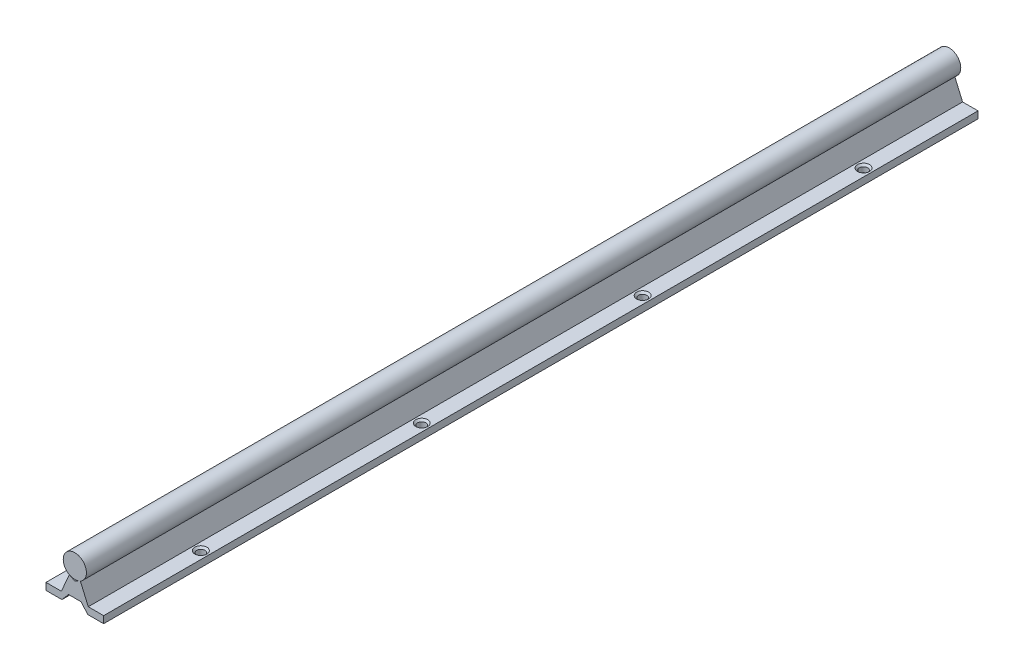
SolidWorks part; units mm, degrees
ref_plane "Front Plane" through (0, 0, 0) normal (0, 0, 1) x (1, 0, 0)
ref_plane "Top Plane" through (0, 0, 0) normal (0, 1, 0) x (1, 0, 0)
ref_plane "Right Plane" through (0, 0, 0) normal (1, 0, 0) x (0, 0, -1)
sketch "Sketch1" plane through (0, 0, 0) normal (0, 0, 1) x (1, 0, 0)
  line L0 (-19.8882, -15.494) -> (-8.89, -15.494)
  line L2 (-4.3688, -10.16) -> (4.3688, -10.16)
  line L4 (8.89, -15.494) -> (19.8882, -15.494)
  line L5 (19.8882, -15.494) -> (19.8882, -10.668)
  line L6 (19.8882, -10.668) -> (9.271, -10.668)
  line L7 (9.271, -10.668) -> (3.81, 1.9814)
  line L8 (3.81, 1.9814) -> (0, 0)
  line L9 (0, 0) -> (-3.81, 1.9814)
  line L10 (-3.81, 1.9814) -> (-9.271, -10.668)
  line L11 (-9.271, -10.668) -> (-19.8882, -10.668)
  line L12 (-19.8882, -10.668) -> (-19.8882, -15.494)
  line L13 (0, 0) -> (0, -10.16) construction
  line L14 (-8.89, -15.494) -> (-4.3688, -10.16)
  line L15 (4.3688, -10.16) -> (8.89, -15.494)
  line L16 (0, 17.018) -> (0, -10.16) construction
  circle A0 centre (0, 9.017) radius 8.001
  dimension "D1" = 16.002
  dimension "D10" = 27.178
  dimension "D2" = 4.826
  dimension "D3" = 39.7764
  dimension "D4" = 5.334
  dimension "D5" = 10.16
  dimension "D6" = 18.542
  dimension "D7" = 7.62
  dimension "D8" = 8.7376
  dimension "D9" = 17.78
extrude "Boss-Extrude1" add sketch "Sketch1" against normal mid plane 603.25 contours L9 A0 L8
sketch "Sketch5" plane through (0, -10.668, 0) normal (0, 1, 0) x (1, 0, 0)
  line L0 (-9.271, -301.625) -> (-19.8882, -301.625) construction
  line L1 (19.8882, -301.625) -> (9.271, -301.625) construction
  circle A0 centre (14.5796, -229.235) radius 2.8702
  circle A1 centre (-14.5796, -229.235) radius 2.8702
  circle A2 centre (-14.5796, -76.835) radius 2.8702
  circle A3 centre (14.5796, -76.835) radius 2.8702
  circle A4 centre (-14.5796, 75.565) radius 2.8702
  circle A5 centre (14.5796, 75.565) radius 2.8702
  circle A6 centre (-14.5796, 227.965) radius 2.8702
  circle A7 centre (14.5796, 227.965) radius 2.8702
  point P7 (-14.5796, -301.625)
  point P10 (14.5796, -301.625)
  dimension "D1" = 5.7404
  dimension "D2" = 72.39
  dimension "D3" = 4
extrude "Cut-Extrude1" cut sketch "Sketch5" against normal through all
chamfer "Chamfer1" distance 1.27 angle 45 8 edges at (11.7094, -10.668, -227.965) (-17.4498, -10.668, -227.965) (11.7094, -10.668, -75.565) (-17.4498, -10.668, -75.565) (11.7094, -10.668, 76.835) (-17.4498, -10.668, 76.835) (11.7094, -10.668, 229.235) (-17.4498, -10.668, 229.235)
